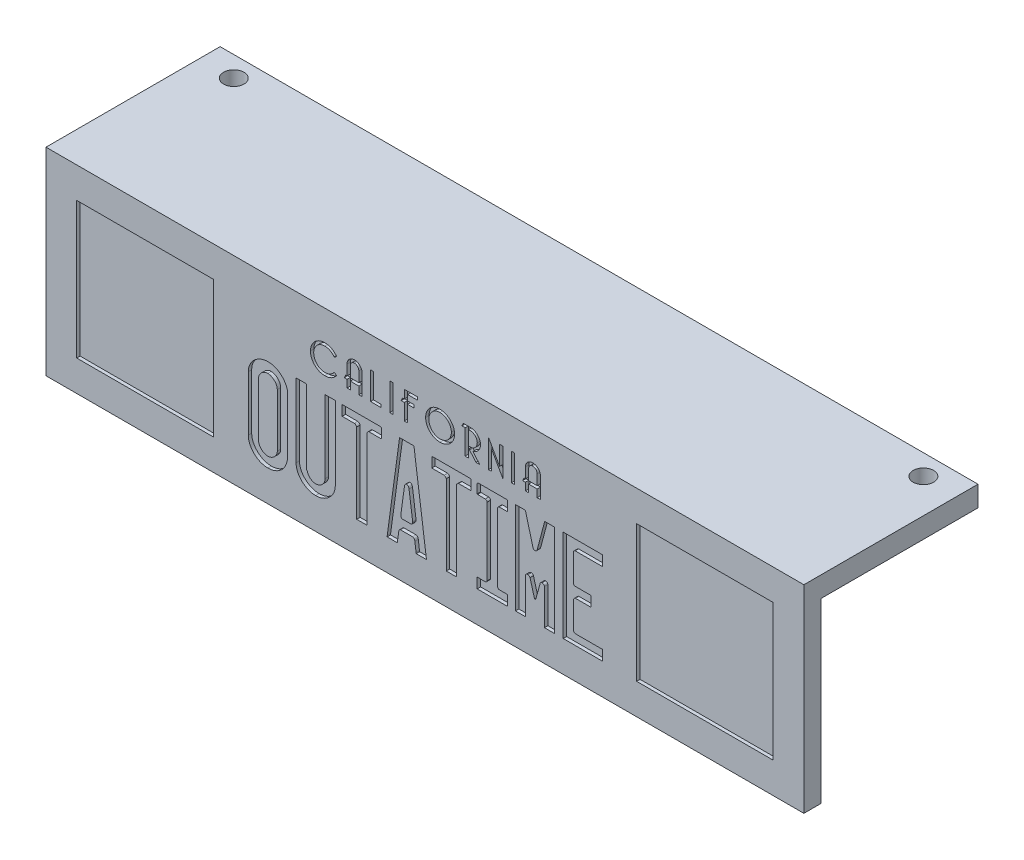
SolidWorks part; units mm, degrees
ref_plane "Front Plane" through (0, 0, 0) normal (0, 0, 1) x (1, 0, 0)
ref_plane "Top Plane" through (0, 0, 0) normal (0, 1, 0) x (1, 0, 0)
ref_plane "Right Plane" through (0, 0, 0) normal (1, 0, 0) x (0, 0, -1)
sketch "Sketch1" plane through (0, 0, 0) normal (0, 1, 0) x (1, 0, 0)
  line L1 (-43.7981, 22.4519) -> (67.2019, 22.4519)
  line L2 (-43.7981, 22.4519) -> (-43.7981, -3.0481)
  line L3 (-43.7981, -3.0481) -> (67.2019, -3.0481)
  line L4 (67.2019, 22.4519) -> (67.2019, -3.0481)
  circle A0 centre (-38.7981, 19.4519) radius 1.5
  circle A1 centre (62.2019, 19.4519) radius 1.5
  dimension "D3" = 3
  dimension "D4" = 101
  dimension "D6" = 5
  dimension "D1" = 25.5
  dimension "D2" = 3
  dimension "D5" = 5
  dimension "D7" = 3
extrude "Boss-Extrude1" add sketch "Sketch1" along normal blind 3
sketch "Sketch3" plane through (0, 0, 0) normal (0, -1, 0) x (1, 0, 0)
  line L0 (67.2019, 3.0481) -> (67.2019, -22.4519) construction
  line L1 (-43.7981, 3.0481) -> (67.2019, 3.0481)
  line L2 (-43.7981, 3.0481) -> (-43.7981, 0.5481)
  line L3 (-43.7981, 0.5481) -> (67.2019, 0.5481)
  line L4 (67.2019, 3.0481) -> (67.2019, 0.5481)
  dimension "D1" = 2.5
extrude "Boss-Extrude2" add sketch "Sketch3" along normal blind 26
sketch "Sketch4" plane through (0, 0, 3.0481) normal (0, 0, 1) x (1, 0, 0)
  line L0 (-43.7981, 3) -> (-43.7981, -26) construction
  line L1 (-39.2981, -1.5) -> (-19.2981, -1.5)
  line L2 (-39.2981, -1.5) -> (-39.2981, -21.5)
  line L3 (-39.2981, -21.5) -> (-19.2981, -21.5)
  line L4 (-19.2981, -1.5) -> (-19.2981, -21.5)
  line L6 (42.7019, -1.5) -> (62.7019, -1.5)
  line L7 (42.7019, -1.5) -> (42.7019, -21.5)
  line L8 (42.7019, -21.5) -> (62.7019, -21.5)
  line L9 (62.7019, -1.5) -> (62.7019, -21.5)
  point P4 (-39.2981, -11.5)
  point P7 (-43.7981, -11.5)
  dimension "D1" = 20
  dimension "D2" = 4.5
  dimension "D3" = 2
extrude "Cut-Extrude1" cut sketch "Sketch4" against normal blind 0.5
ref_plane "Plane2" through (-43.7981, 0, 0.5481) normal (1, 0, 0) x (0, 0, -1)
sketch "Sketch6" plane through (-43.7981, 0, 0.5481) normal (1, 0, 0) x (0, 0, -1)
  line L0 (0, 0) -> (5, 0)
  line L1 (23, 0) -> (0, 0) construction
  line L2 (5, 0) -> (0, -13)
  line L3 (0, -26) -> (0, 0) construction
  line L4 (0, -13) -> (0, 0)
  dimension "D1" = 5
extrude "Boss-Extrude3" add sketch "Sketch6" along normal blind 4 from offset 20.5
pattern_linear "LPattern1" count 4 spacing 22 along (1, 0, 0) of "Boss-Extrude3"
sketch "Sketch8" plane through (0, 0, 3.0481) normal (0, 0, 1) x (1, 0, 0)
  line L0 (-43.7981, -21.4493) -> (67.2019, -21.4493) construction
  line L1 (-43.7981, 3) -> (-43.7981, -26) construction
  line L2 (67.2019, 3) -> (67.2019, -26) construction
  line L3 (-43.7981, -5.5) -> (67.2019, -5.5) construction
  line L6 (-19.2981, -1.5) -> (-39.2981, -1.5) construction
  text T0 "OUTATIME" font "LICENSE PLATE USA" height 13.5
  text T1 "<b>CALIFORNIA</b>" font "Bellerose" height 4
  dimension "D1" = 4
extrude "Cut-Extrude3" cut sketch "Sketch8" against normal blind 0.5
